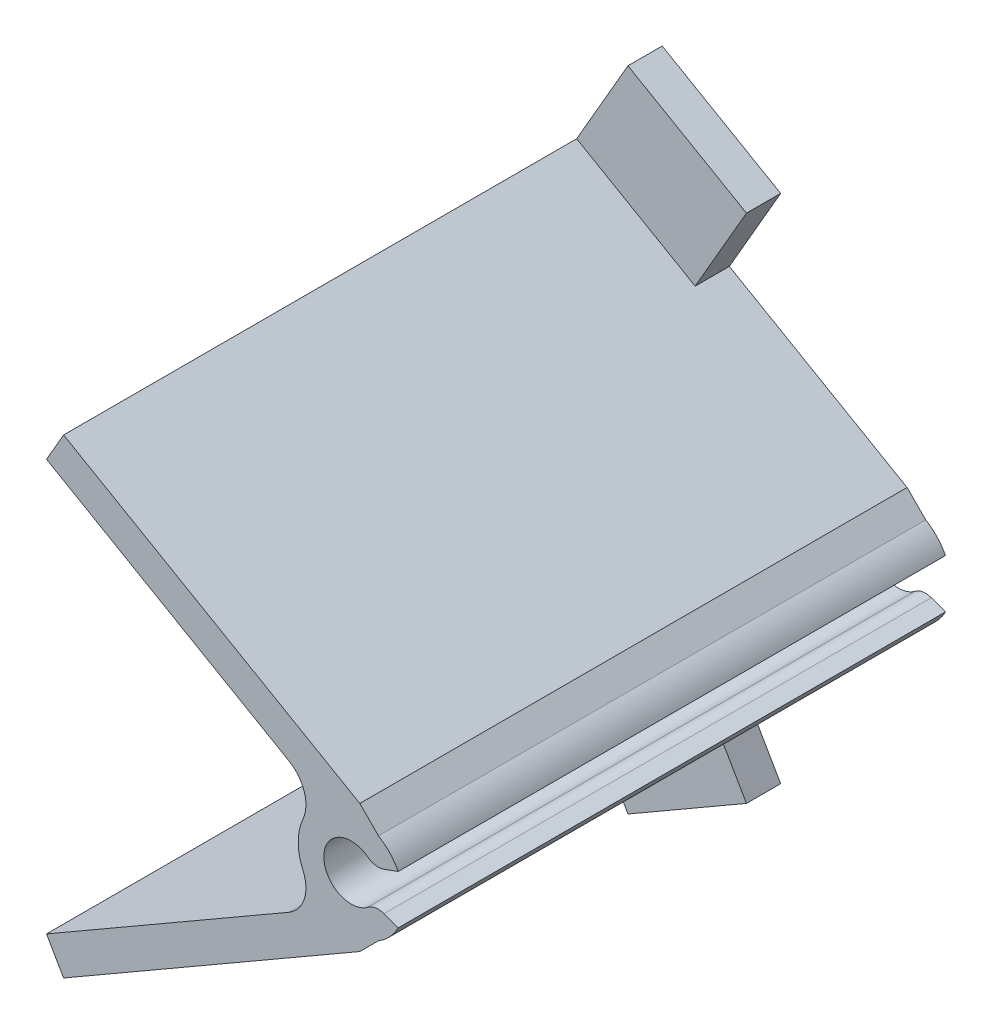
SolidWorks part; units mm, degrees
ref_plane "Front Plane" through (0, 0, 0) normal (0, 0, 1) x (1, 0, 0)
ref_plane "Top Plane" through (0, 0, 0) normal (0, 1, 0) x (1, 0, 0)
ref_plane "Right Plane" through (0, 0, 0) normal (1, 0, 0) x (0, 0, -1)
sketch "Sketch5" plane through (4.2285, 0, 0) normal (0, 0, 1) x (1, 0, 0)
  line L0 (2.2783, -2.5811) -> (-4.2285, -0.2128) construction
  line L1 (2.2783, 2.5811) -> (-4.2285, 0.2128) construction
  line L2 (-3.569, 0.4529) -> (-2.8525, 0.7136)
  line L3 (-2.8525, -0.7136) -> (-3.569, -0.4529)
  line L12 (-4.2285, 0) -> (3.1715, 0) construction
  line L22 (-4.2285, 0) -> (2.3494, -2.3941) construction
  arc A1 (-2.8525, 0.7136) -> (-2.8525, -0.7136) centre (-4.2285, 0) ccw
  arc A2 (-3.569, 0.4529) -> (-3.569, -0.4529) centre (-4.2285, 0) ccw
  circle A3 centre (-4.2285, 0) radius 7 construction
  dimension "D1" = 0.2
  dimension "D6" = 0.75
  dimension "D8" = 0.8
  dimension "D2" = 14
  dimension "D9" = 20
extrude "Boss-Extrude2" add sketch "Sketch5" along normal blind 16 separate body
sketch "Sketch6" plane through (0, 0, 16) normal (0, 0, 1) x (1, 0, 0)
  line L0 (0, 0) -> (-2.8397, 0) construction
  line L1 (1.5, 0) -> (-13.6302, 8.7354) construction
  line L2 (-8.9074, 6.0087) -> (-8.4074, 6.8747)
  line L3 (-8.4074, 6.8747) -> (0.2528, 1.8747)
  line L4 (0, 0) -> (1.5, 0) construction
  line L5 (-8.9074, 6.0087) -> (0.1144, 0.8)
  line L6 (0.2528, -1.8747) -> (1.3276, -0.8)
  line L7 (-8.9074, -6.0087) -> (-8.4074, -6.8747)
  line L8 (-8.9074, -6.0087) -> (0.1144, -0.8)
  line L9 (1.3276, -0.8) -> (0.1144, -0.8)
  line L10 (-8.4074, -6.8747) -> (0.2528, -1.8747)
  line L11 (-2.8397, 0.8) -> (4.5784, 0.8) construction
  line L12 (0.2528, 1.8747) -> (1.3276, 0.8)
  line L13 (1.3276, 0.8) -> (0.1144, 0.8)
  arc A0 (0.6595, 0.4529) -> (0.6595, -0.4529) centre (0, 0) ccw construction
  arc A1 (1.3759, 0.7136) -> (1.3759, -0.7136) centre (0, 0) ccw construction
  dimension "D1" = 1
  dimension "D2" = 10
  dimension "D3" = 30
  dimension "D4" = 1.5
  dimension "D5" = 45
extrude "Boss-Extrude3" add sketch "Sketch6" against normal up to surface (16 mm away) up to face at (-0.0786, 0, 0)
fillet "Fillet9" radius 0.5 2 edges at (0.6595, -0.4529, 8) (0.6595, 0.4529, 8)
sketch "Sketch7" plane through (0, 0, 0) normal (0, 0, -1) x (-1, 0, 0)
  line L0 (8.4074, 6.8747) -> (4.9433, 4.8747)
  line L1 (8.4074, 6.8747) -> (6.9074, 9.4728)
  line L2 (4.9433, 4.8747) -> (3.4433, 7.4728)
  line L3 (6.9074, 9.4728) -> (3.4433, 7.4728)
  line L4 (8.4074, 6.8747) -> (-0.2528, 1.8747) construction
  line L5 (0, 0) -> (7.4941, 0) construction
  line L6 (6.9074, -9.4728) -> (3.4433, -7.4728)
  line L7 (4.9433, -4.8747) -> (3.4433, -7.4728)
  line L8 (8.4074, -6.8747) -> (6.9074, -9.4728)
  line L9 (8.4074, -6.8747) -> (4.9433, -4.8747)
  line L10 (8.9074, 6.0087) -> (7.1754, 5.0087)
  line L11 (8.9074, 6.0087) -> (9.4074, 5.1427)
  line L12 (7.1754, 5.0087) -> (7.6754, 4.1427)
  line L13 (9.4074, 5.1427) -> (7.6754, 4.1427)
  line L14 (0.7997, 1.3278) -> (8.9074, 6.0087) construction
  line L15 (9.4074, -5.1427) -> (7.6754, -4.1427)
  line L16 (7.1754, -5.0087) -> (7.6754, -4.1427)
  line L17 (8.9074, -6.0087) -> (9.4074, -5.1427)
  line L18 (8.9074, -6.0087) -> (7.1754, -5.0087)
  dimension "D1" = 4
  dimension "D2" = 3
  dimension "D3" = 1
  dimension "D4" = 2
extrude "Boss-Extrude4" add sketch "Sketch7" against normal blind 1
fillet "Fillet10" radius 1 2 edges at (-0.7997, -1.3278, 8) (-0.7997, 1.3278, 8)
